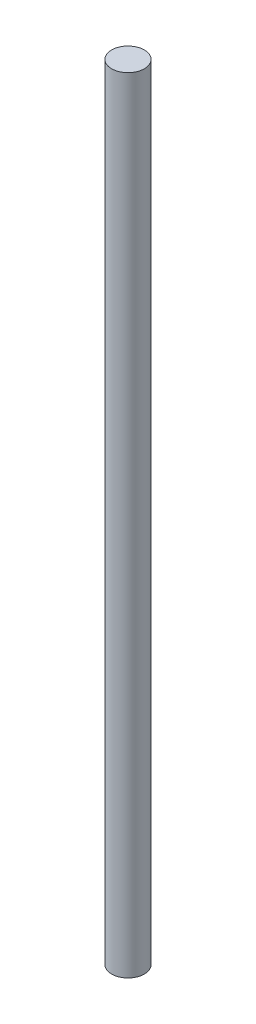
SolidWorks part; units mm, degrees
ref_plane "Front Plane" through (0, 0, 0) normal (0, 0, 1) x (1, 0, 0)
ref_plane "Top Plane" through (0, 0, 0) normal (0, 1, 0) x (1, 0, 0)
ref_plane "Right Plane" through (0, 0, 0) normal (1, 0, 0) x (0, 0, -1)
sketch "Sketch1" plane through (0, 0, 0) normal (0, 1, 0) x (1, 0, 0)
  circle A0 centre (0, 0) radius 1.5875
  dimension "D1" = 3.175
extrude "Boss-Extrude1" add sketch "Sketch1" along normal blind 76.2
